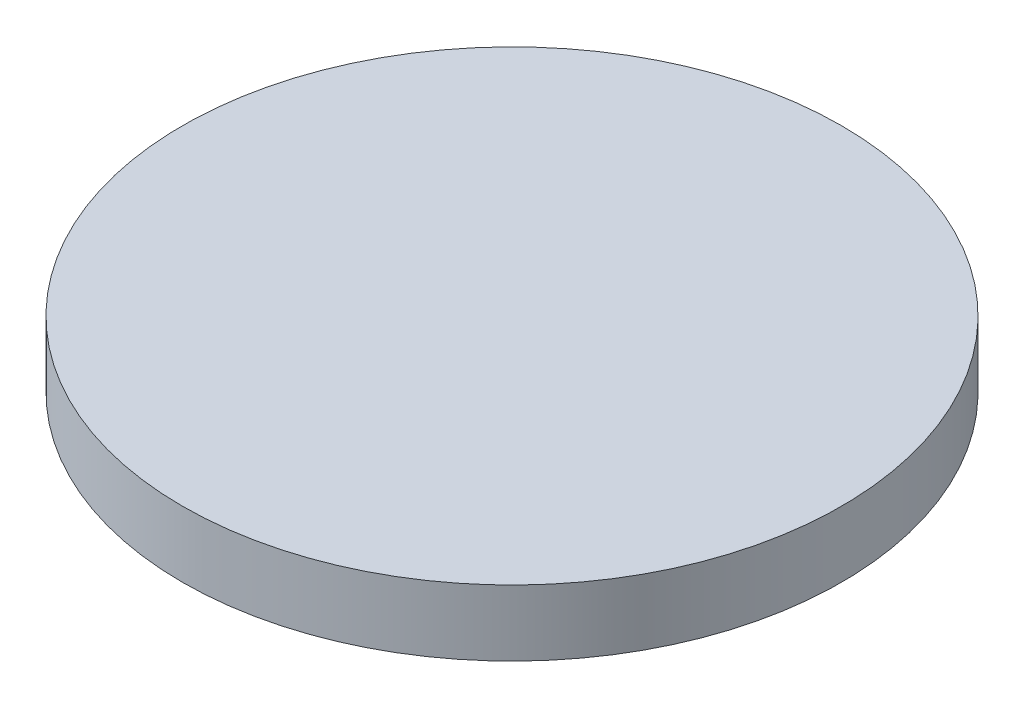
SolidWorks part; units mm, degrees
ref_plane "Face" through (0, 0, 0) normal (0, 0, 1) x (1, 0, 0)
ref_plane "Dessus" through (0, 0, 0) normal (0, 1, 0) x (1, 0, 0)
ref_plane "Droite" through (0, 0, 0) normal (1, 0, 0) x (0, 0, -1)
sketch "Esquisse1" plane through (0, 0, 0) normal (0, 1, 0) x (1, 0, 0)
  circle A0 centre (0, 0) radius 50
  dimension "D1" = 100
extrude "Extrusion1" add sketch "Esquisse1" along normal blind 10
